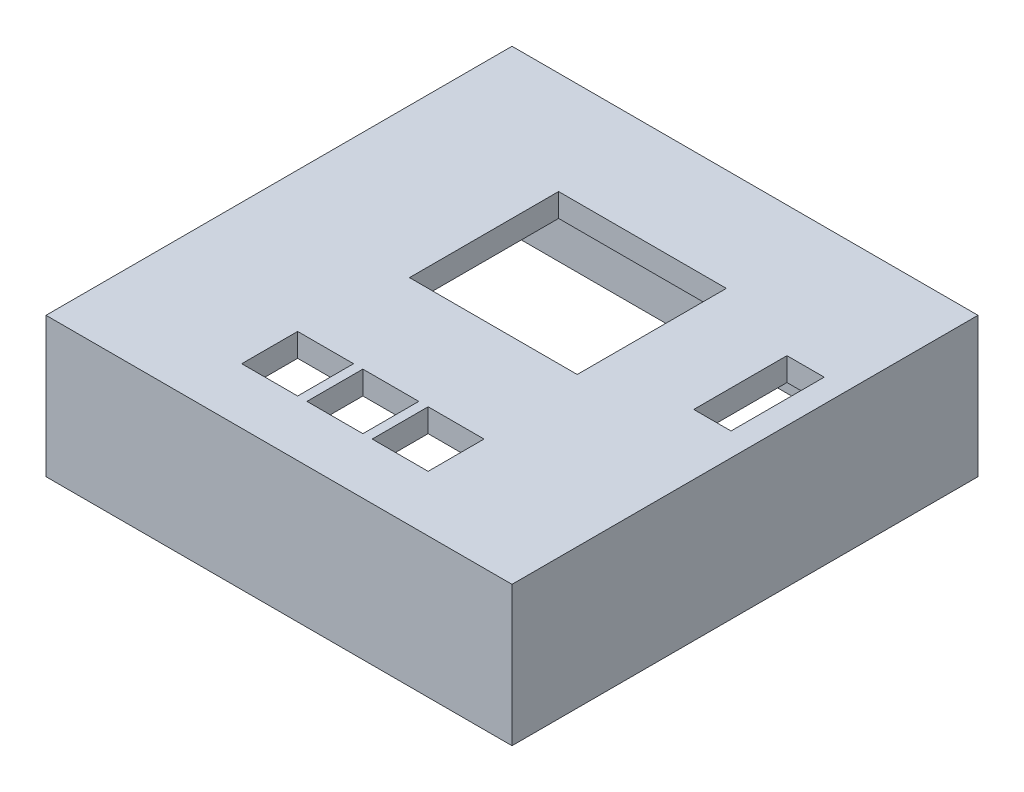
SolidWorks part; units mm, degrees
ref_plane "Front Plane" through (0, 0, 0) normal (0, 0, 1) x (1, 0, 0)
ref_plane "Top Plane" through (0, 0, 0) normal (0, 1, 0) x (1, 0, 0)
ref_plane "Right Plane" through (0, 0, 0) normal (1, 0, 0) x (0, 0, -1)
sketch "Sketch1" plane through (0, 0, 0) normal (0, 1, 0) x (1, 0, 0)
  line L1 (50, -50) -> (-50, -50)
  line L2 (50, -50) -> (50, 50)
  line L3 (50, 50) -> (-50, 50)
  line L4 (-50, -50) -> (-50, 50)
  line L5 (50, -50) -> (-50, 50) construction
  line L6 (50, 50) -> (-50, -50) construction
  point P0 (0, 0)
  dimension "D1" = 100
extrude "Boss-Extrude1" add sketch "Sketch1" along normal blind 30
shell "Shell2" thickness 5
sketch "Sketch2" plane through (0, 30, 0) normal (0, 1, 0) x (1, 0, 0)
  line L4 (-50, 50) -> (-50, -50)
  line L5 (-50, -50) -> (50, -50)
  line L6 (50, -50) -> (50, 50)
  line L7 (50, 50) -> (-50, 50)
  line L8 (-50, 50) -> (-50, -50)
  line L9 (-50, -50) -> (50, -50)
  line L10 (50, -50) -> (50, 50)
  line L11 (50, 50) -> (-50, 50)
  dimension "D1" = 0
extrude "Boss-Extrude2" add sketch "Sketch2" along normal blind 5
sketch "Sketch3" plane through (0, 35, 0) normal (0, 1, 0) x (1, 0, 0)
  line L0 (-50, 50) -> (-50, -50) construction
  line L1 (-20, -26) -> (-8, -26)
  line L2 (-20, -26) -> (-20, -38)
  line L3 (-20, -38) -> (-8, -38)
  line L4 (-8, -26) -> (-8, -38)
  line L5 (-20, -26) -> (-8, -38) construction
  line L6 (-20, -38) -> (-8, -26) construction
  line L7 (-50, -50) -> (50, -50) construction
  line L8 (-6, -26) -> (6, -26)
  line L9 (-6, -26) -> (-6, -38)
  line L10 (-6, -38) -> (6, -38)
  line L11 (6, -26) -> (6, -38)
  line L12 (-6, -26) -> (6, -38) construction
  line L13 (-6, -38) -> (6, -26) construction
  line L14 (8, -26) -> (20, -26)
  line L15 (8, -26) -> (8, -38)
  line L16 (8, -38) -> (20, -38)
  line L17 (20, -26) -> (20, -38)
  line L18 (8, -26) -> (20, -38) construction
  line L19 (8, -38) -> (20, -26) construction
  line L20 (0, 0) -> (0, 24) construction
  line L22 (-18, 28) -> (18, 28)
  line L23 (-18, 28) -> (-18, -4)
  line L24 (-18, -4) -> (18, -4)
  line L25 (18, 28) -> (18, -4)
  line L26 (-18, 28) -> (18, -4) construction
  line L27 (-18, -4) -> (18, 28) construction
  line L28 (18, 12) -> (50, 12) construction
  line L29 (37, 22) -> (45, 22)
  line L30 (37, 22) -> (37, 2)
  line L31 (37, 2) -> (45, 2)
  line L32 (45, 22) -> (45, 2)
  line L33 (37, 22) -> (45, 2) construction
  line L34 (37, 2) -> (45, 22) construction
  line L35 (50, -50) -> (50, 50) construction
  point P0 (-14, -32)
  point P9 (0, -32)
  point P14 (14, -32)
  point P19 (0, 12)
  point P28 (41, 12)
  point P36 (0, 0)
  dimension "D1" = 30
  dimension "D2" = 12
  dimension "D3" = 12
  dimension "D4" = 12
  dimension "D5" = 2
  dimension "D6" = 12
  dimension "D7" = 2
  dimension "D8" = 12
  dimension "D9" = 12
  dimension "D10" = 12
  dimension "D11" = 32
  dimension "D12" = 36
  dimension "D13" = 12
  dimension "D14" = 8
  dimension "D15" = 20
  dimension "D16" = 5
extrude "Cut-Extrude1" cut sketch "Sketch3" against normal blind 5
sketch "Sketch5" plane through (-50, 0, 0) normal (-1, 0, 0) x (0, 0, 1)
  line L0 (50, 35) -> (50, 0) construction
  line L1 (35, 30) -> (45, 30)
  line L2 (35, 30) -> (35, 20)
  line L3 (35, 20) -> (45, 20)
  line L4 (45, 30) -> (45, 20)
  line L5 (-50, 0) -> (50, 0) construction
  dimension "D1" = 10
  dimension "D2" = 10
  dimension "D3" = 5
  dimension "D4" = 20
extrude "Cut-Extrude2" cut sketch "Sketch5" against normal blind 5
sketch "Sketch6" plane through (0, 0, -50) normal (0, 0, -1) x (-1, 0, 0)
  line L0 (50, 35) -> (50, 0) construction
  line L1 (11, 30) -> (40, 30)
  line L2 (11, 30) -> (11, 20)
  line L3 (11, 20) -> (40, 20)
  line L4 (40, 30) -> (40, 20)
  line L5 (-50, 0) -> (50, 0) construction
  dimension "D1" = 10
  dimension "D2" = 20
  dimension "D3" = 29
  dimension "D4" = 10
extrude "Cut-Extrude3" cut sketch "Sketch6" against normal blind 5
sketch "Sketch8" plane through (0, 0, 0) normal (0, -1, 0) x (1, 0, 0)
  line L4 (-50, 50) -> (-50, -50)
  line L5 (-50, -50) -> (50, -50)
  line L6 (50, -50) -> (50, 50)
  line L7 (50, 50) -> (-50, 50)
  line L8 (-50, 50) -> (-50, -50)
  line L9 (-50, -50) -> (50, -50)
  line L10 (50, -50) -> (50, 50)
  line L11 (50, 50) -> (-50, 50)
  dimension "D1" = 0
extrude "Cut-Extrude4" cut sketch "Sketch8" against normal blind 5
hole_wizard "Ø4.0mm Dowel Hole1" positions "3DSketch2" profile "Sketch11" hole size "Ø4.0" standard "ISO"
sketch3d "3DSketch2"
  line L0 (-50, 5, 50) -> (-50, 5, -50) construction
  line L1 (50, 5, 50) -> (-50, 5, 50) construction
  line L2 (50, 5, -50) -> (50, 5, 50) construction
  line L3 (-50, 5, -50) -> (50, 5, -50) construction
  point P0 (-47.5, 5, 46)
  point P2 (47.5, 5, 46)
  point P4 (47.5, 5, -46)
  point P6 (-47.5, 5, -46)
  dimension "D1" = 2.5
  dimension "D2" = 4
  dimension "D3" = 4
  dimension "D4" = 2.5
  dimension "D5" = 4
  dimension "D6" = 2.5
  dimension "D7" = 2.5
  dimension "D8" = 4
sketch "Sketch11" plane through (-47.5, 5, 46) normal (1, 0, 0) x (0, 0, -1)
  line L0 (0, 0) -> (0, 6.2017)
  line L1 (0, 6.2017) -> (2, 5)
  line L2 (2, 5) -> (2, 0)
  line L5 (2, 0) -> (0, 0)
  line L10 (0, 6.2017) -> (-2, 5) construction
  line L11 (0, -6.35) -> (0, 107.95) construction
  dimension "Hole Dia." = 4
  dimension "Hole Depth" = 5
  dimension "Drill Angle" = 118
